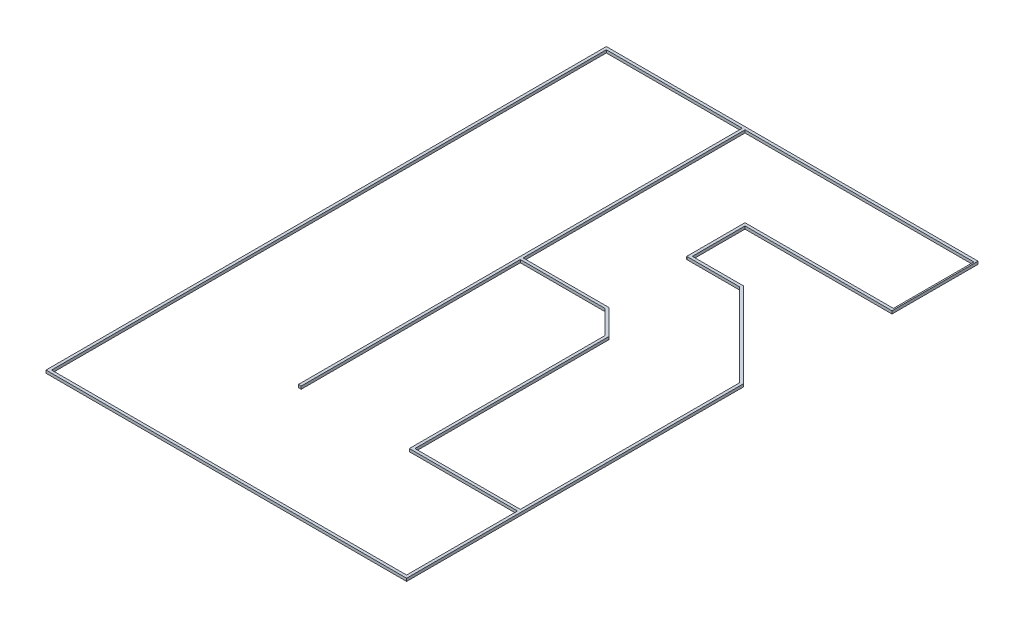
SolidWorks part; units mm, degrees
material "6063-O"
ref_plane "Front Plane" through (0, 0, 0) normal (0, 0, 1) x (1, 0, 0)
ref_plane "Top Plane" through (0, 0, 0) normal (0, 1, 0) x (1, 0, 0)
ref_plane "Right Plane" through (0, 0, 0) normal (1, 0, 0) x (0, 0, -1)
sketch "Sketch1" plane through (0, 0, 0) normal (0, 1, 0) x (1, 0, 0)
  line L0 (-225, 4170.5146) -> (-1725, 5670.5146)
  line L1 (0, 8170.5146) -> (-6625, 8170.5146)
  line L2 (-6625, 8170.5146) -> (-6625, -1829.4854)
  line L3 (-6625, -1829.4854) -> (-225, -1829.4854)
  line L4 (-225, -1829.4854) -> (-225, 4170.5146)
  line L5 (-1725, 5670.5146) -> (-2675, 5670.5146)
  line L6 (-2675, 5670.5146) -> (-2675, 6720.5146)
  line L7 (-2675, 6720.5146) -> (0, 6720.5146)
  line L8 (0, 8220.5146) -> (-6675, 8220.5146)
  line L9 (-6675, 8220.5146) -> (-6675, -1879.4854)
  line L10 (-6675, -1879.4854) -> (-175, -1879.4854)
  line L11 (-175, -1879.4854) -> (-175, 4191.2253)
  line L12 (-175, 4191.2253) -> (-1704.2893, 5720.5146)
  line L13 (-1704.2893, 5720.5146) -> (-2625, 5720.5146)
  line L14 (-2625, 5720.5146) -> (-2625, 6670.5146)
  line L15 (-2625, 6670.5146) -> (0, 6670.5146)
  line L16 (0, 8220.5146) -> (0, 8170.5146)
  line L17 (0, 6720.5146) -> (0, 6670.5146)
  line L18 (-4125, 4170.5146) -> (-2575, 4170.5146)
  line L19 (0, 8220.5146) -> (25, 8220.5146)
  line L20 (0, 8220.5146) -> (0, 6670.5146)
  line L21 (0, 6670.5146) -> (25, 6670.5146)
  line L22 (25, 8220.5146) -> (25, 6670.5146)
  line L23 (-4175, 8170.5146) -> (-4125, 8170.5146)
  line L24 (-4175, 8170.5146) -> (-4175, 170.5146)
  line L25 (-4175, 170.5146) -> (-4125, 170.5146)
  line L26 (-4125, 8170.5146) -> (-4125, 170.5146)
  line L27 (-2575, 4170.5146) -> (-2125, 3720.5146)
  line L28 (-2125, 3720.5146) -> (-2125, 170.5146)
  line L29 (-4125, 4120.5146) -> (-2595.7107, 4120.5146)
  line L30 (-2595.7107, 4120.5146) -> (-2175, 3699.8039)
  line L31 (-2175, 3699.8039) -> (-2175, 170.5146)
  line L32 (-2175, 170.5146) -> (-2125, 170.5146)
  line L33 (-4125, 4170.5146) -> (-4125, 4120.5146)
  line L35 (-2125, 170.5146) -> (-225, 170.5146)
  line L36 (-2125, 170.5146) -> (-2125, 220.5146)
  line L37 (-2125, 220.5146) -> (-225, 220.5146)
  line L38 (-225, 170.5146) -> (-225, 220.5146)
  dimension "D1" = 6625
  dimension "D2" = 10000
  dimension "D3" = 6400
  dimension "D4" = 6000
  dimension "D5" = 2675
  dimension "D6" = 1500
  dimension "D7" = 1050
  dimension "D9" = 25
  dimension "D10" = 1550
  dimension "D11" = 50
  dimension "D12" = 8000
  dimension "D13" = 0
  dimension "D14" = 2450
  dimension "D15" = 135
  dimension "D16" = 450
  dimension "D17" = 3550
  dimension "D18" = 0
  dimension "D19" = 2000
  dimension "D21" = 50
  dimension "D8" = 50
  dimension "D20" = 50
extrude "Boss-Extrude1" add sketch "Sketch1" along normal blind 50.8 contours L17 L7 L6 L5 L0 L4 L3 L2 L1 L16 L8 L9 L10 L11 L12 L13 L14 L15 | L22 L19 L16 L20 L17 L21 | L26 L1 L24 L25 | L31 L32 L28 L27 L18 L26 L29 L30 | L37 L28 L35 L4
